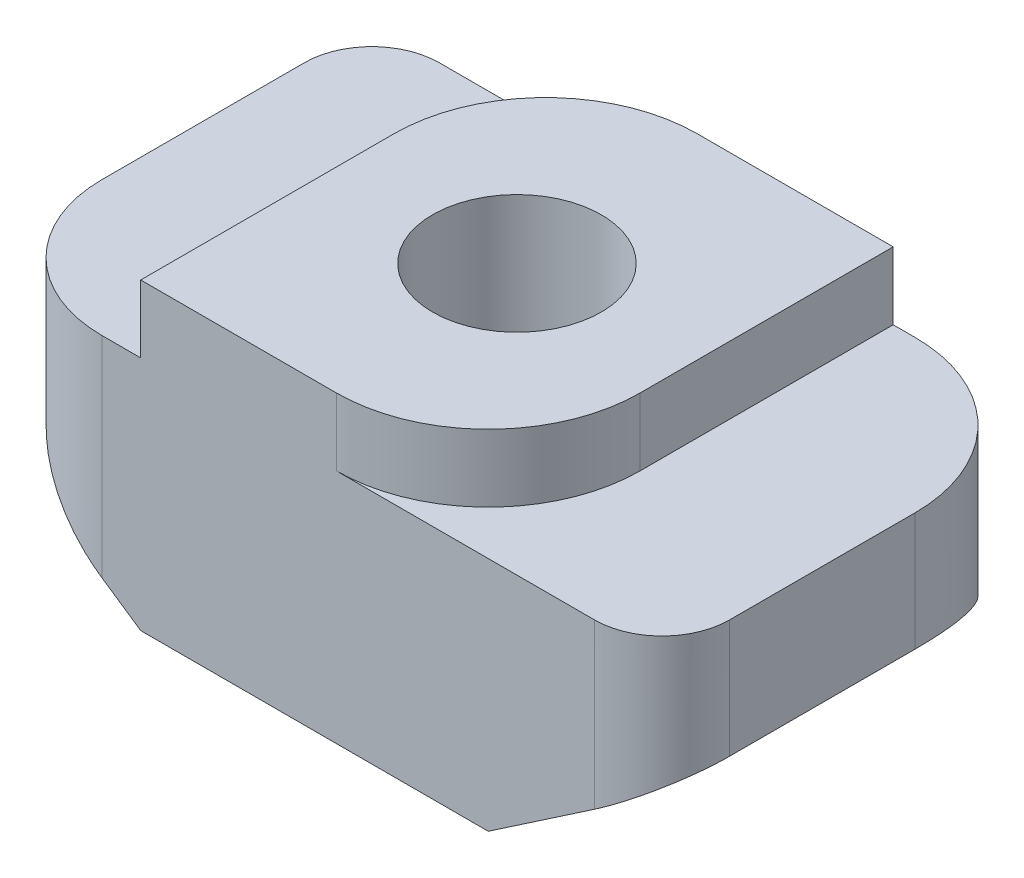
SolidWorks part; units mm, degrees
ref_plane "Front Plane" through (0, 0, 0) normal (0, 0, 1) x (1, 0, 0)
ref_plane "Top Plane" through (0, 0, 0) normal (0, 1, 0) x (1, 0, 0)
ref_plane "Right Plane" through (0, 0, 0) normal (1, 0, 0) x (0, 0, -1)
sketch "Sketch1" plane through (0, 0, 0) normal (0, 0, 1) x (1, 0, 0)
  line L0 (0, 2.5) -> (0, -2.5) construction
  line L1 (-5.15, 1.75) -> (-2.575, 1.75)
  line L2 (-5.15, 1.75) -> (-5.15, 0)
  line L3 (-2.575, -1.75) -> (2.575, -1.75)
  line L4 (5.15, 1.75) -> (5.15, 0)
  line L5 (-5.15, 1.75) -> (3.4333, -1.1667) construction
  line L6 (-3.4333, -1.1667) -> (5.15, 1.75) construction
  line L7 (0, 0) -> (-5.15, 0) construction
  line L8 (-2.575, 1.75) -> (-2.575, -1.75) construction
  line L9 (-5.15, 0) -> (-2.575, -1.75)
  line L10 (5.15, 0) -> (2.575, -1.75)
  line L11 (-2.575, 1.75) -> (-2.575, 2.75)
  line L12 (-2.575, 2.75) -> (2.575, 2.75)
  line L13 (2.575, 2.75) -> (2.575, 1.75)
  line L14 (2.575, 1.75) -> (5.15, 1.75)
  point P0 (0, 0)
  point P13 (-2.575, 0)
  dimension "D1" = 10.3
  dimension "D2" = 4.5
  dimension "D3" = 1
extrude "Boss-Extrude1" add sketch "Sketch1" along normal blind 6
sketch "Sketch2" plane through (0, 2.75, 0) normal (0, 1, 0) x (1, 0, 0)
  line L0 (0, 0) -> (0, -6) construction
  line L1 (2.575, -6) -> (-2.575, -6) construction
  point P5 (0, -3)
hole_wizard "M3x0.5 Tapped Hole1" positions "Sketch3" profile "Sketch4" tap size "M3x0.5" standard "ANSI Metric" end condition through all
sketch "Sketch3" plane through (0, 2.75, 0) normal (0, 1, 0) x (1, 0, 0)
  point P0 (0, -3)
sketch "Sketch4" plane through (0, 2.75, 3) normal (1, 0, 0) x (0, 0, 1)
  line L0 (0, 0) -> (0, 4.5)
  line L1 (0, 4.5) -> (1.25, 4.5)
  line L2 (1.25, 4.5) -> (1.25, 0)
  line L5 (1.25, 0) -> (0, 0)
  line L11 (0, -6.35) -> (0, 107.95) construction
  dimension "Thru Tap Drill Dia." = 2.5
  dimension "Thru Tap Drill Depth" = 4.5
cosmetic thread "Hole Thread1" parameters "D2"=3
fillet "Fillet1" radius 1 1 edges at (-5.15, 0.875, 0)
fillet "Fillet2" radius 2 1 edges at (-5.15, 0.875, 6)
fillet "Fillet3" radius 1 1 edges at (5.15, 0.875, 6)
fillet "Fillet4" radius 2.25 1 edges at (5.15, 0.875, 0)
fillet "Fillet5" radius 2.25 2 edges at (-2.575, 2.25, 0) (2.575, 2.25, 6)
